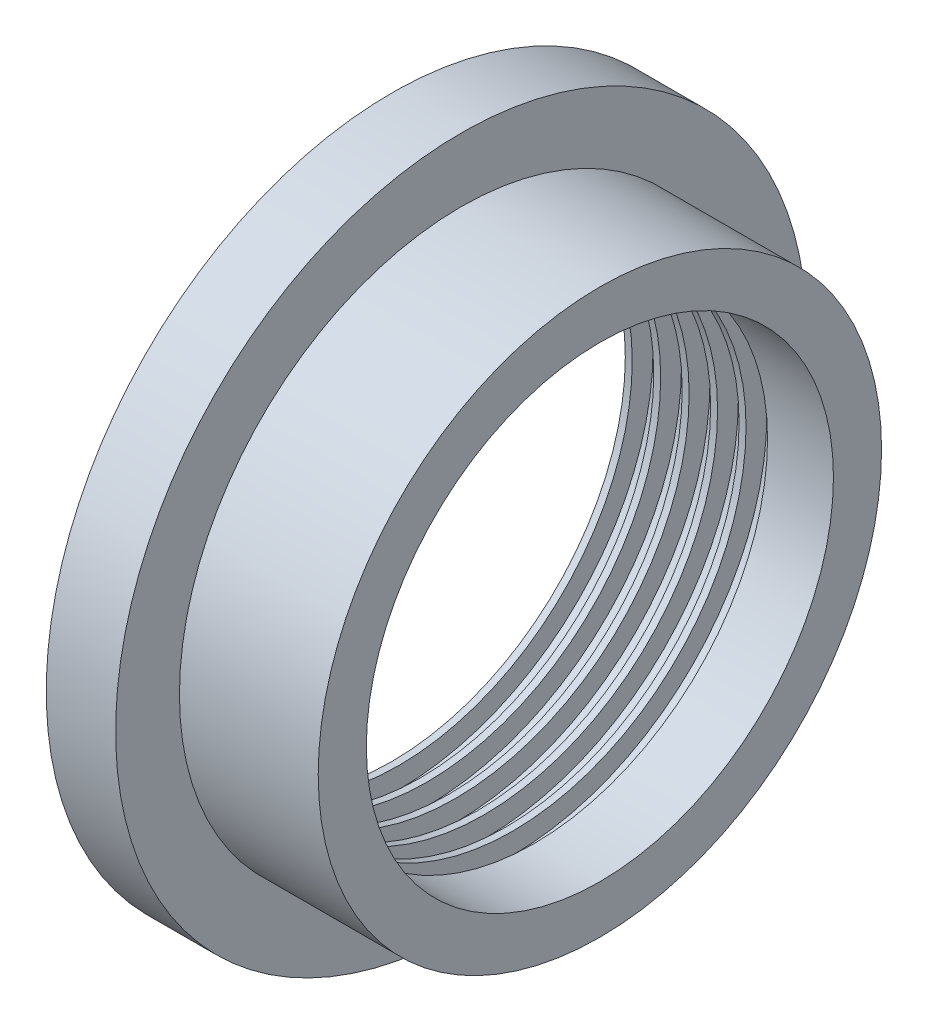
SolidWorks part; units mm, degrees
ref_plane "Front Plane" through (0, 0, 0) normal (0, 0, 1) x (1, 0, 0)
ref_plane "Top Plane" through (0, 0, 0) normal (0, 1, 0) x (1, 0, 0)
ref_plane "Right Plane" through (0, 0, 0) normal (1, 0, 0) x (0, 0, -1)
sketch "Sketch1" plane through (0, 0, 0) normal (0, 0, 1) x (1, 0, 0)
  line L0 (-7.62, 12.6492) -> (-7.62, 8.5508)
  line L2 (0, 8.5508) -> (0, 10.3124)
  line L4 (-5.08, 10.3124) -> (-5.08, 12.6492)
  line L5 (-5.08, 12.6492) -> (-7.62, 12.6492)
  line L10 (-7.62, 8.5508) -> (-7.366, 8.5508)
  line L11 (-7.366, 8.5508) -> (-7.366, 9.3128)
  line L12 (-7.366, 9.3128) -> (-6.5786, 9.3128)
  line L13 (-6.5786, 9.3128) -> (-6.5786, 8.5508)
  line L14 (-6.5786, 8.5508) -> (-6.3246, 8.5508)
  line L15 (-6.3246, 8.5508) -> (-6.3246, 9.3128)
  line L16 (-6.3246, 9.3128) -> (-5.5372, 9.3128)
  line L17 (-5.5372, 9.3128) -> (-5.5372, 8.5508)
  line L18 (-5.5372, 8.5508) -> (-5.2832, 8.5508)
  line L19 (-5.2832, 8.5508) -> (-5.2832, 9.3128)
  line L20 (-5.2832, 9.3128) -> (-4.4958, 9.3128)
  line L21 (-4.4958, 9.3128) -> (-4.4958, 8.5508)
  line L22 (-4.4958, 8.5508) -> (-4.2418, 8.5508)
  line L23 (-4.2418, 8.5508) -> (-4.2418, 9.3128)
  line L24 (-4.2418, 9.3128) -> (-3.4544, 9.3128)
  line L25 (-3.4544, 9.3128) -> (-3.4544, 8.5508)
  line L26 (-3.4544, 8.5508) -> (-3.2004, 8.5508)
  line L27 (-3.2004, 8.5508) -> (-3.2004, 9.3128)
  line L28 (-3.2004, 9.3128) -> (-2.413, 9.3128)
  line L29 (-2.413, 9.3128) -> (-2.413, 8.5508)
  line L30 (-2.413, 8.5508) -> (0, 8.5508)
  line L31 (0, 0) -> (-7.2739, 0) construction
  line L33 (-5.08, 10.3124) -> (0, 10.3124)
  line L34 (0, 0) -> (0, 8.5508) construction
  dimension "D1" = 0.7874
  dimension "D2" = 0.254
  dimension "D3" = 0.762
  dimension "D4" = 8.5508
  dimension "D6" = 12.6492
  dimension "D5" = 7.62
  dimension "D7" = 10.3124
  dimension "D8" = 2.54
revolve "Revolve1" add sketch "Sketch1" angle 360 about L31
equation "\"Cavity_Depth\" = 0.031in"
equation "\"Cavity_Width\" = 0.031in"
equation "\"D1@Sketch1\"=\"Cavity_Width\""
equation "\"Tooth_Width\" = .01in"
equation "\"D2@Sketch1\"=\"Tooth_Width\""
equation "\"Shaft_Seal_OD\"= 17mm'diameter at seal area"
equation "\"Shaft_clearance\"= .002in"
equation "\"D4@Sketch1\"=\"Shaft_Seal_OD\"/2 +\"Shaft_clearance\""
equation "\"O-Ring_ID\"= .801in"
equation "\"O-Ring_CS\"= .070in"
equation "\"Shaft_OD\"= .5in"
